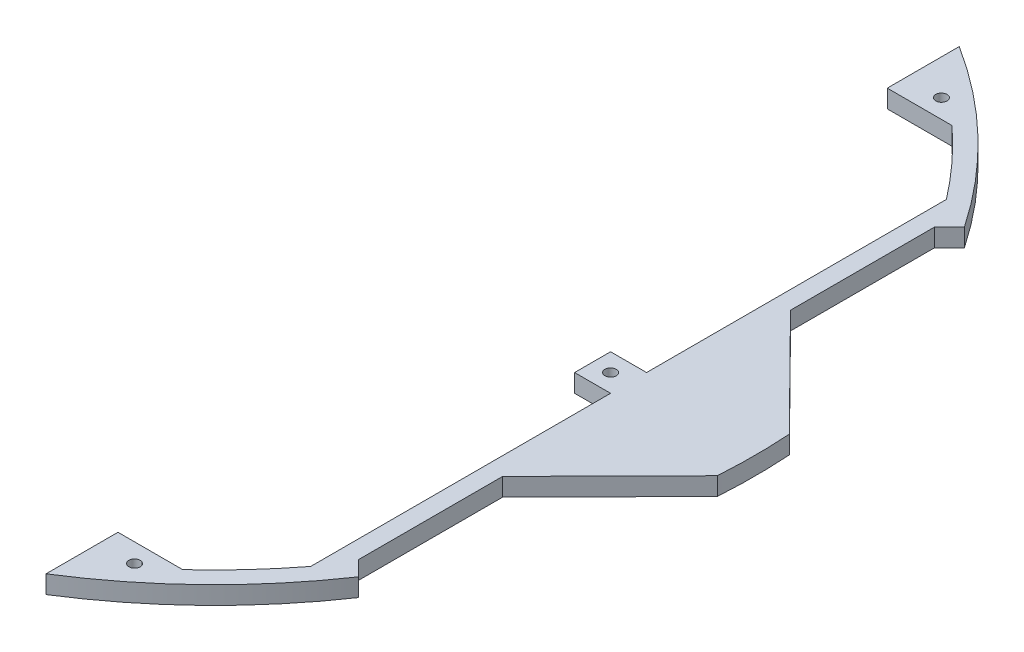
SolidWorks part; units mm, degrees
ref_plane "Front Plane" through (0, 0, 0) normal (0, 0, 1) x (1, 0, 0)
ref_plane "Top Plane" through (0, 0, 0) normal (0, 1, 0) x (1, 0, 0)
ref_plane "Right Plane" through (0, 0, 0) normal (1, 0, 0) x (0, 0, -1)
sketch "Sketch1" plane through (0, 0, 0) normal (0, 1, 0) x (1, 0, 0)
  line L0 (152.4, -101.6) -> (152.4, -50.8)
  line L1 (0, 0) -> (127, 0) construction
  line L2 (133.35, 6.35) -> (133.35, -6.35)
  line L3 (25.4, 0) -> (25.4, 38.1)
  line L4 (25.4, 38.1) -> (25.4, 114.3)
  line L5 (146.05, 6.35) -> (146.05, 112.1634)
  line L6 (101.6, 161.1449) -> (101.6, 135.7449)
  line L7 (101.6, -135.7449) -> (124.4369, -135.7449)
  line L8 (0, 0) -> (152.4, 0) construction
  line L9 (101.6, 63.5) -> (152.4, 63.5) construction
  line L10 (101.6, -135.7449) -> (101.6, -161.1449)
  line L11 (152.4, 50.8) -> (190.0762, 12.7)
  line L12 (146.05, -6.35) -> (146.05, -112.1634)
  line L13 (101.6, 135.7449) -> (124.4369, 135.7449)
  line L14 (161.1449, 101.6) -> (202.8194, 101.6)
  line L15 (152.4, 50.8) -> (152.4, 101.6)
  line L16 (152.4, 101.6) -> (157.6874, 106.8874)
  line L17 (152.4, -101.6) -> (157.6874, -106.8874)
  line L18 (152.4, -50.8) -> (190.0762, -12.7)
  line L23 (133.35, -6.35) -> (146.05, -6.35)
  line L28 (133.35, 6.35) -> (146.05, 6.35)
  arc A0 (152.4, 114.3) -> (152.4, -114.3) centre (0, 0) ccw construction
  arc A1 (146.05, 112.1634) -> (124.4369, 135.7449) centre (0, 0) ccw construction
  arc A2 (101.6, -161.1449) -> (152.4, -114.3) centre (0, 0) ccw
  arc A3 (124.4369, -135.7449) -> (146.05, -112.1634) centre (0, 0) ccw
  arc A4 (146.05, 112.1634) -> (124.4369, 135.7449) centre (0, 0) ccw
  arc A5 (152.4, 114.3) -> (101.6, 161.1449) centre (0, 0) ccw
  arc A6 (116.785, 142.3815) -> (101.6, -153.586) centre (0, 0) ccw construction
  arc A7 (124.4369, -135.7449) -> (146.05, -112.1634) centre (0, 0) ccw construction
  arc A8 (157.6874, 106.8874) -> (161.1449, 101.6) centre (0, 0) ccw construction
  arc A9 (157.6874, 106.8874) -> (152.4, 114.3) centre (0, 0) ccw
  arc A10 (190.0762, -12.7) -> (190.0762, 12.7) centre (0, 0) ccw
  arc A11 (157.6874, -106.8874) -> (152.4, -114.3) centre (0, 0) cw
  point P37 (101.6, 63.5)
  point P67 (101.6, -63.5)
  point P91 (0, 0)
  dimension "D10" = 25.4
  dimension "D6" = 127
  dimension "D5" = 381
  dimension "D9" = 368.3
  dimension "D2" = 25.4
  dimension "D3" = 38.1
  dimension "D4" = 76.2
  dimension "D7" = 152.4
  dimension "D8" = 6.35
  dimension "D11" = 22.8369
  dimension "D12" = 25.4
  dimension "D13" = 12.7
  dimension "D14" = 12.7
  dimension "D15" = 50.8
  dimension "D16" = 63.5
  dimension "D17" = 50.8
  dimension "D18" = 12.7
  dimension "D19" = 12.7
extrude "Boss-Extrude2" add sketch "Sketch1" along normal blind 6.35 contours L23 L12 A3 L7 L10 A2 A11 L17 L0 L18 A10 L11 L15 L16 A9 A5 L6 L13 A4 L5 L28 L2
sketch "Sketch40" plane through (0, 6.35, 0) normal (0, 1, 0) x (1, 0, 0)
  circle A0 centre (139.7, 0) radius 2
  dimension "D1" = 4
extrude "Cut-Extrude1" cut sketch "Sketch40" against normal blind 6.35
sketch "Sketch41" plane through (0, 6.35, 0) normal (0, 1, 0) x (1, 0, 0)
  line L0 (0, 0) -> (126.5613, 142.3815)
  line L1 (0, 0) -> (102.1784, 0)
  line L2 (126.5613, 142.3815) -> (94.4992, 142.3815)
  arc A0 (157.6874, 106.8874) -> (101.6, 161.1449) centre (0, 0) ccw construction
  circle A1 centre (114.0807, 142.3815) radius 2
  circle A2 centre (114.0807, -142.3815) radius 2
  dimension "D3" = 4
  dimension "D1" = 48.366
  dimension "D2" = 12.4807
extrude "Cut-Extrude2" cut sketch "Sketch41" against normal blind 6.35 contours A2 | A1
